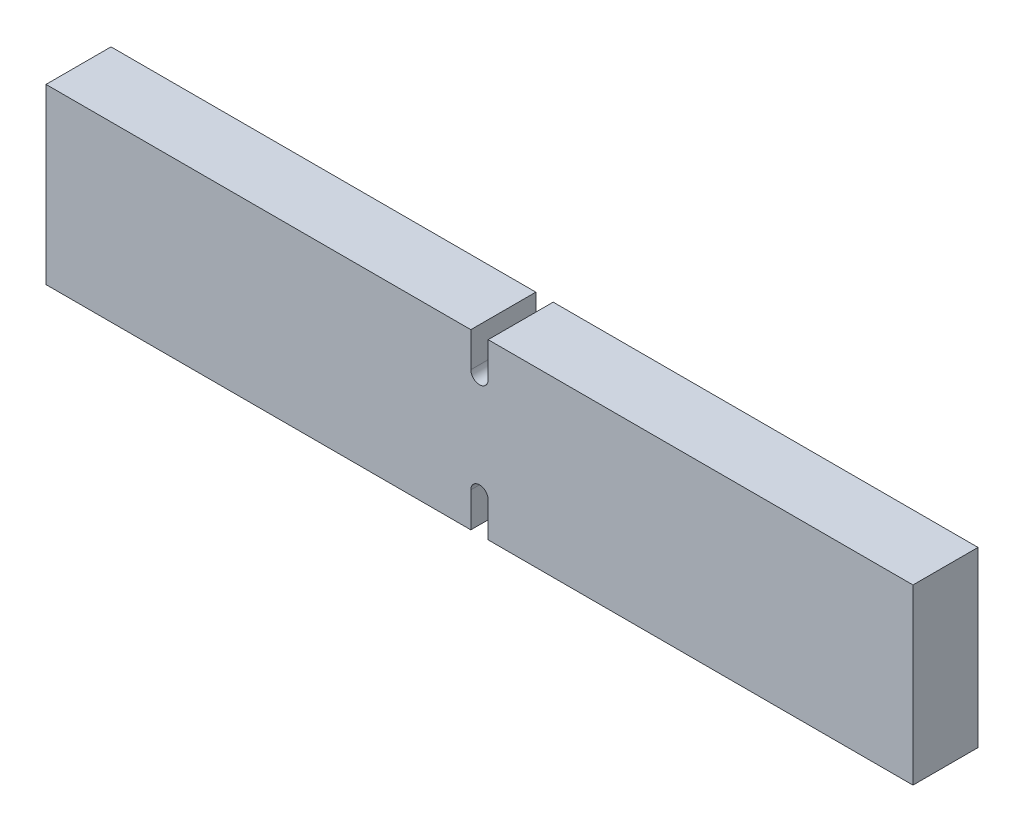
SolidWorks part; units mm, degrees
ref_plane "Front" through (0, 0, 0) normal (0, 0, 1) x (1, 0, 0)
ref_plane "Top" through (0, 0, 0) normal (0, 1, 0) x (1, 0, 0)
ref_plane "Right" through (0, 0, 0) normal (1, 0, 0) x (0, 0, -1)
sketch "Sketch1" plane through (0, 0, 0) normal (0, 0, 1) x (1, 0, 0)
  line L1 (-100, 20) -> (100, 20)
  line L2 (-100, 20) -> (-100, -20)
  line L3 (-100, -20) -> (100, -20)
  line L4 (100, 20) -> (100, -20)
  dimension "D1" = 200
  dimension "D2" = 40
  dimension "D3" = 20
  dimension "D4" = 100
extrude "Rectangular Bar (40 W x 200 L x 15D)" add sketch "Sketch1" along normal blind 15
sketch "Notch" plane through (0, 0, 15) normal (0, 0, 1) x (1, 0, 0)
  line L0 (2, 20) -> (2, 12)
  line L1 (100, 20) -> (-100, 20) construction
  line L2 (-2, -20) -> (-2, -12)
  line L3 (-2, 20) -> (-2, 12)
  line L4 (-100, -20) -> (100, -20) construction
  line L5 (2, -20) -> (2, -12)
  line L6 (-2, -20) -> (2, -20)
  line L7 (-2, 20) -> (2, 20)
  arc A0 (2, 12) -> (-2, 12) centre (0, 12) cw
  arc A1 (-2, -12) -> (2, -12) centre (0, -12) cw
  dimension "D2" = 2
  dimension "D4" = 8
  dimension "D1" = 8
  dimension "D3" = 2
  dimension "D5" = 8
extrude "Notch cut out" cut sketch "Notch" against normal blind 15
